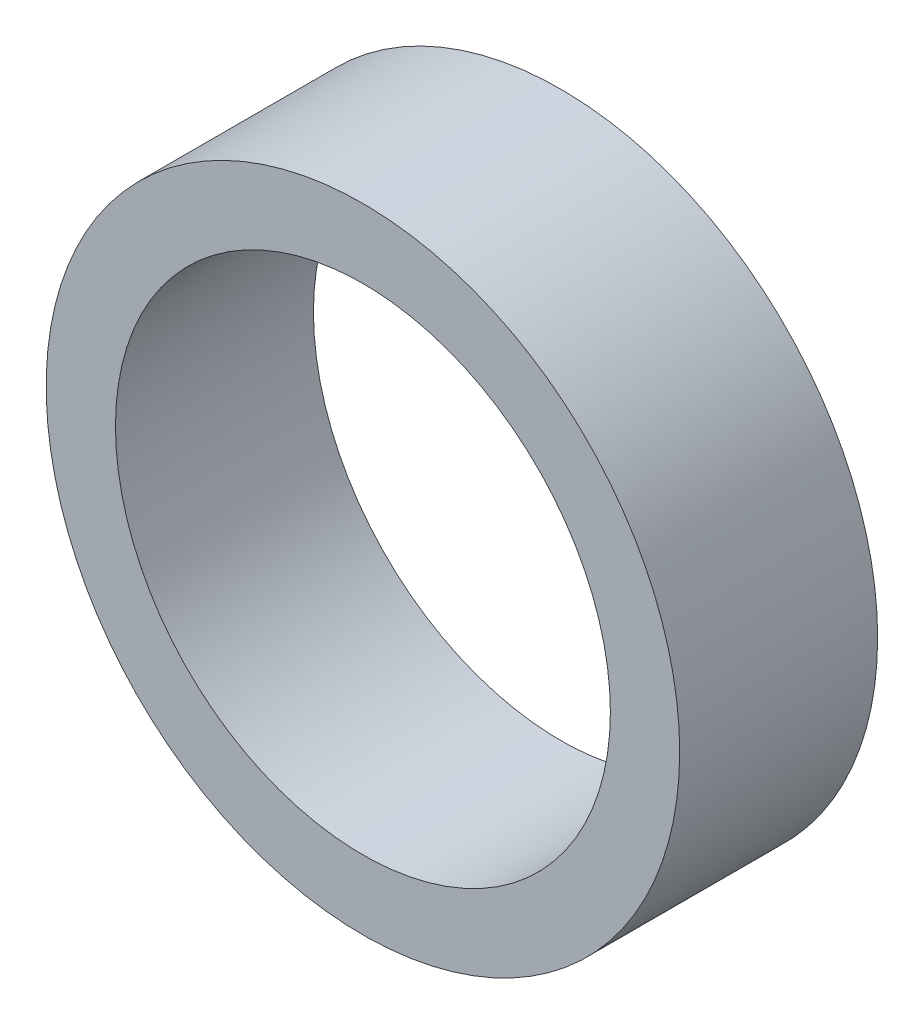
SolidWorks part; units mm, degrees
ref_plane "前视基准面" through (0, 0, 0) normal (0, 0, 1) x (1, 0, 0)
ref_plane "上视基准面" through (0, 0, 0) normal (0, 1, 0) x (1, 0, 0)
ref_plane "右视基准面" through (0, 0, 0) normal (1, 0, 0) x (0, 0, -1)
sketch "草图1" plane through (0, 0, 0) normal (0, 0, 1) x (1, 0, 0)
  circle A0 centre (0, 0) radius 4
  circle A1 centre (0, 0) radius 3.125
  dimension "D1" = 8
  dimension "D2" = 6.25
extrude "凸台-拉伸1" add sketch "草图1" along normal blind 2.5
